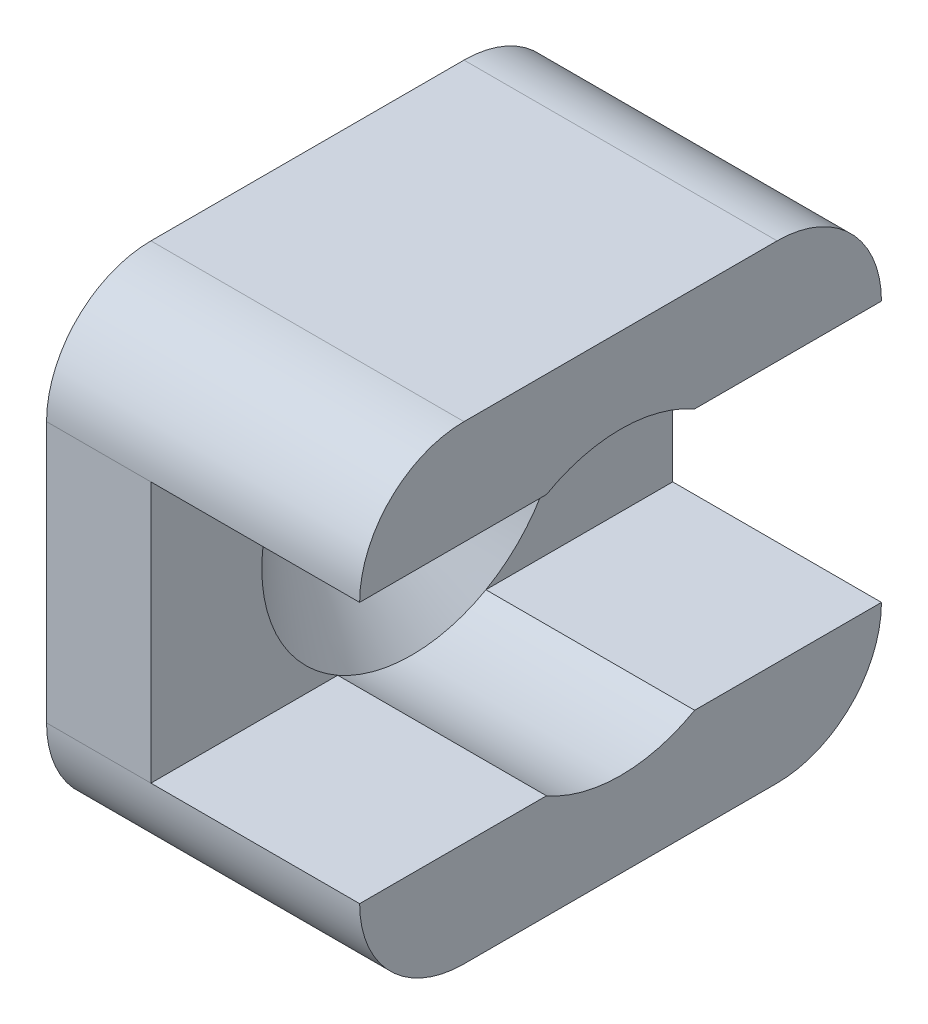
SolidWorks part; units mm, degrees
ref_plane "Plan de face" through (0, 0, 0) normal (0, 0, 1) x (1, 0, 0)
ref_plane "Plan de dessus" through (0, 0, 0) normal (0, 1, 0) x (1, 0, 0)
ref_plane "Plan de droite" through (0, 0, 0) normal (1, 0, 0) x (0, 0, -1)
ref_plane "Plan1" through (8.0788, 0, 0) normal (1, 0, 0) x (0, 0, -1)
sketch "Esquisse1" plane through (8.0788, 0, 0) normal (1, 0, 0) x (0, 0, -1)
  line L0 (-20, 1.8) -> (0, 1.8)
  line L1 (0, 1.8) -> (0, 19.8)
  line L2 (0, 19.8) -> (-20, 19.8)
  line L3 (-20, 19.8) -> (-20, 1.8)
extrude "Boss.-Extru.1" add sketch "Esquisse1" against normal blind 12
sketch "Esquisse2" plane through (0, 0, 0) normal (0, 0, -1) x (-1, 0, 0)
  line L0 (-8.0788, 5.8) -> (-0.0788, 5.8)
  line L1 (-0.0788, 5.8) -> (-0.0788, 15.8)
  line L2 (-0.0788, 15.8) -> (-8.0788, 15.8)
  line L3 (-8.0788, 15.8) -> (-8.0788, 5.8)
extrude "Enlèv. mat.-Extru.1" cut sketch "Esquisse2" against normal through all
sketch "Esquisse3" plane through (8.0788, 0, 0) normal (1, 0, 0) x (0, 0, -1)
  line L0 (-20, 1.8) -> (0, 1.8) construction
  line L1 (-20, 5.8) -> (-20, 15.8) construction
  circle A1 centre (-10, 10.8) radius 5.75
  dimension "D1" = 11.5
  dimension "D2" = 10
  dimension "D3" = 9
extrude "Enlèv. mat.-Extru.2" cut sketch "Esquisse3" against normal blind 8
ref_plane "Plan2" through (0, 0, 10) normal (0, 0, -1) x (-1, 0, 0)
sketch "Esquisse5" plane through (0, 0, 10) normal (0, 0, -1) x (-1, 0, 0)
  line L0 (-0.0788, 16.55) -> (-0.0788, 10.8)
  line L1 (-0.0788, 10.8) -> (3.9212, 10.8)
  line L2 (3.9212, 10.8) -> (3.9212, 13.55)
  line L3 (3.9212, 13.55) -> (2.9212, 13.55)
  line L4 (2.9212, 13.55) -> (-0.0788, 16.55)
  line L5 (-0.0788, 10.8) -> (3.9212, 10.8) construction
  line L6 (3.9212, 1.8) -> (-8.0788, 1.8) construction
  dimension "D1" = 2.75
  dimension "D2" = 9
  dimension "D3" = 45
  dimension "D4" = 5.75
  dimension "D5" = 1
revolve "Enlèvement de matière-Révolution1" cut sketch "Esquisse5" angle 360 about L5
fillet "Congé2" radius 4 4 edges at (2.0788, 1.8, 20) (2.0788, 19.8, 0) (2.0788, 1.8, 0) (2.0788, 19.8, 20)
